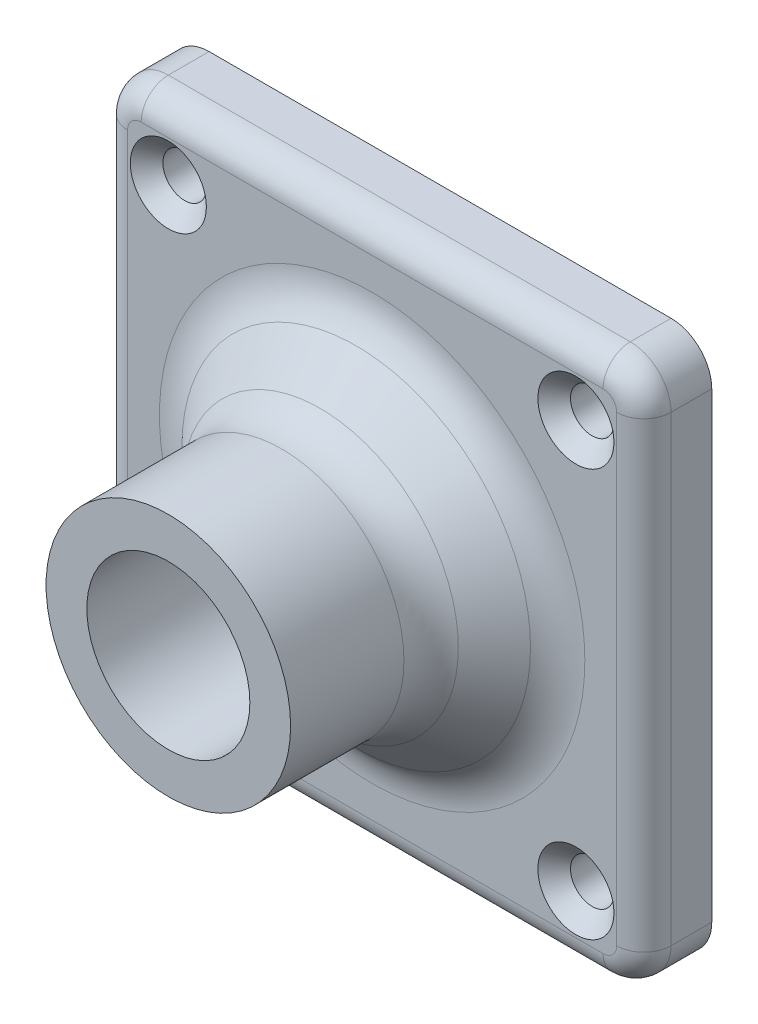
SolidWorks part; units mm, degrees
ref_plane "Front Plane" through (0, 0, 0) normal (0, 0, 1) x (1, 0, 0)
ref_plane "Top Plane" through (0, 0, 0) normal (0, 1, 0) x (1, 0, 0)
ref_plane "Right Plane" through (0, 0, 0) normal (1, 0, 0) x (0, 0, -1)
sketch "Sketch2" plane through (0, 0, 0) normal (0, 0, 1) x (1, 0, 0)
  circle A0 centre (-135, -82.3127) radius 6
  circle A1 centre (-135, -82.3127) radius 9
extrude "Boss-Extrude1" add sketch "Sketch2" along normal blind 20
sketch "Sketch3" plane through (0, 0, 0) normal (0, 0, -1) x (-1, 0, 0)
  line L1 (152, -102.3127) -> (118, -102.3127)
  line L2 (155, -99.3127) -> (155, -65.3127)
  line L3 (152, -62.3127) -> (118, -62.3127)
  line L4 (115, -99.3127) -> (115, -65.3127)
  circle A0 centre (135, -82.3127) radius 6
  arc A5 (118, -102.3127) -> (115, -99.3127) centre (118, -99.3127) cw
  arc A6 (152, -102.3127) -> (155, -99.3127) centre (152, -99.3127) ccw
  arc A7 (155, -65.3127) -> (152, -62.3127) centre (152, -65.3127) ccw
  arc A8 (118, -62.3127) -> (115, -65.3127) centre (118, -65.3127) ccw
  point P8 (115, -102.3127)
  point P11 (155, -102.3127)
  point P14 (155, -62.3127)
  dimension "D1" = 20
  dimension "D5" = 3
  dimension "D2" = 40
  dimension "D3" = 40
  dimension "D4" = 20
extrude "Boss-Extrude2" add sketch "Sketch3" against normal blind 5
fillet "Fillet1" radius 2 8 edges at (-154.1213, -101.434, 5) (-135, -102.3127, 5) (-115.8787, -101.434, 5) (-115, -82.3127, 5) (-115.8787, -63.1913, 5) (-135, -62.3127, 5) (-154.1213, -63.1913, 5) (-155, -82.3127, 5)
sketch "Sketch4" plane through (0, 0, 5) normal (0, 0, 1) x (1, 0, 0)
  line L2 (-135, -62.3127) -> (-135, -102.3127) construction
  line L3 (-152, -62.3127) -> (-118, -62.3127) construction
  line L4 (-118, -102.3127) -> (-152, -102.3127) construction
  line L5 (-155, -82.3127) -> (-115, -82.3127) construction
  line L6 (-155, -99.3127) -> (-155, -65.3127) construction
  line L7 (-115, -65.3127) -> (-115, -99.3127) construction
  circle A0 centre (-150, -67.3127) radius 1.6
  circle A1 centre (-120, -67.3127) radius 1.6
  circle A2 centre (-120, -97.3127) radius 1.6
  circle A3 centre (-150, -97.3127) radius 1.6
extrude "Cut-Extrude1" cut sketch "Sketch4" against normal up to surface (7 mm away)
chamfer "Chamfer1" distance 5 angle 45 1 edges at (-126, -82.3127, 5)
fillet "Fillet2" radius 4 2 edges at (-126, -82.3127, 10) (-121, -82.3127, 5)
chamfer "Chamfer2" distance 1.2 angle 45 4 edges at (-148.4, -67.3127, 5) (-121.6, -67.3127, 5) (-118.4, -97.3127, 5) (-151.6, -97.3127, 5)
